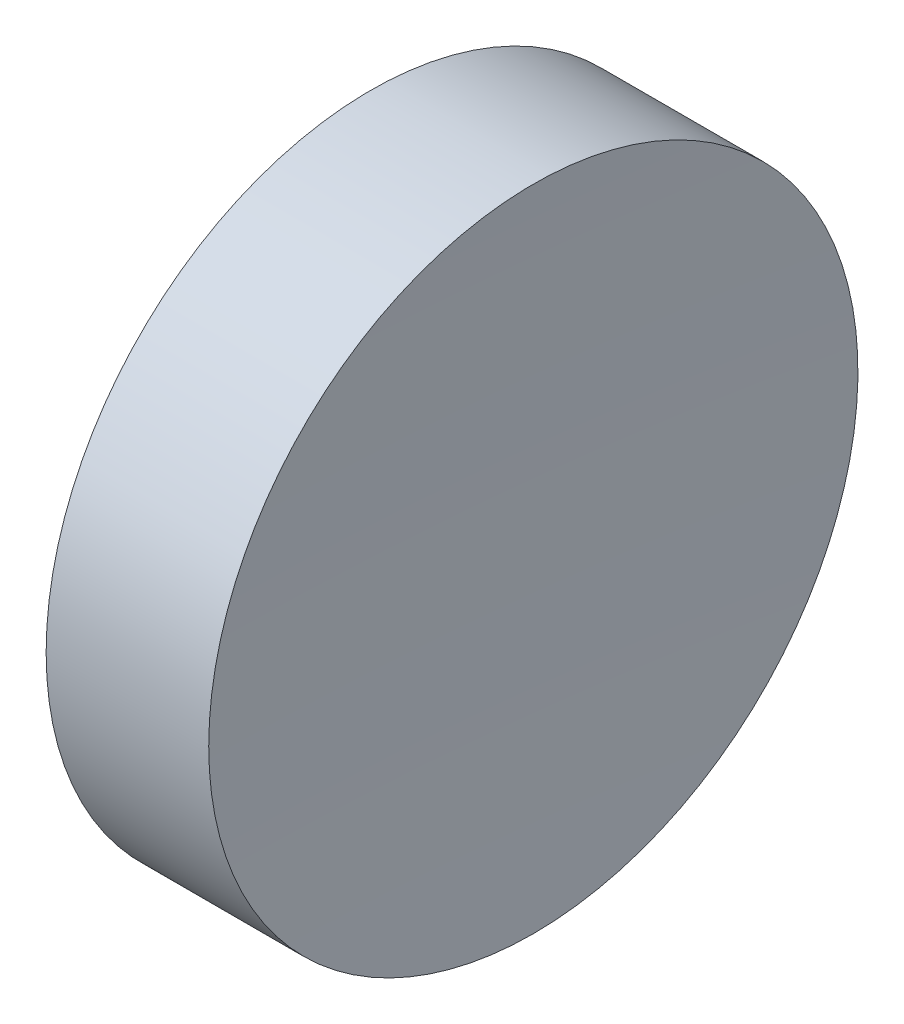
SolidWorks part; units mm, degrees
ref_plane "前视基准面" through (0, 0, 0) normal (0, 0, 1) x (1, 0, 0)
ref_plane "上视基准面" through (0, 0, 0) normal (0, 1, 0) x (1, 0, 0)
ref_plane "右视基准面" through (0, 0, 0) normal (1, 0, 0) x (0, 0, -1)
sketch "草图1" plane through (0, 0, 0) normal (0, 0, 1) x (1, 0, 0)
  line L0 (54.4926, 34.689) -> (66.3882, 34.689) construction
  line L1 (57.5463, 34.689) -> (57.5463, 40.939)
  line L2 (57.5463, 40.939) -> (60.6766, 40.939)
  line L3 (60.5463, 34.689) -> (57.5463, 34.689)
  arc A0 (60.6766, 40.939) -> (60.5463, 34.689) centre (210.5463, 34.689) ccw
  dimension "D2" = 150
  dimension "D1" = 3.1303
revolve "旋转1" add sketch "草图1" angle 360 about L0
